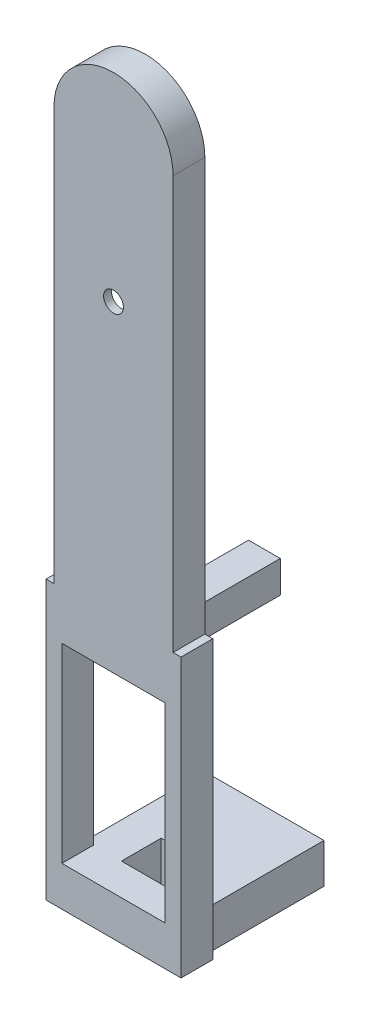
SolidWorks part; units mm, degrees
ref_plane "前基準面" through (0, 0, 0) normal (0, 0, 1) x (1, 0, 0)
ref_plane "上基準面" through (0, 0, 0) normal (0, 1, 0) x (1, 0, 0)
ref_plane "右基準面" through (0, 0, 0) normal (1, 0, 0) x (0, 0, -1)
sketch "草圖1" plane through (0, 0, 0) normal (0, 0, 1) x (1, 0, 0)
  line L0 (0, 0) -> (0, 4.6483) construction
  line L1 (7.5, 0) -> (7.5, 52)
  line L2 (7.5, 0) -> (-7.5, 0)
  line L3 (-7.5, 0) -> (-7.5, 52)
  arc A0 (7.5, 52) -> (-7.5, 52) centre (0, 52) ccw
  dimension "D1" = 7.5
  dimension "D2" = 52
extrude "填料-伸長1" add sketch "草圖1" along normal blind 4
sketch "草圖3" plane through (0, 0, 0) normal (0, 0, 1) x (1, 0, 0)
  line L0 (0, 0) -> (0, 14.8578) construction
  line L1 (7.5, 52) -> (-7.5, 52) construction
  line L2 (7.5, 15) -> (-7.5, 15) construction
  line L3 (7.5, 0) -> (7.5, 52) construction
  line L4 (-7.5, 52) -> (-7.5, 0) construction
  line L6 (7.5, 34.5) -> (5, 34.5) construction
  line L7 (5, 34.5) -> (2.1147, 16.658)
  line L8 (5, 34.5) -> (2.1328, 52)
  line L9 (-2.1328, 52) -> (-5, 34.5)
  line L10 (-5, 34.5) -> (-2.1422, 17)
  line L11 (0, 54.1328) -> (0, 59.5) construction
  line L12 (-5, 34.5) -> (-7.5, 34.5) construction
  arc A0 (7.5, 52) -> (-7.5, 52) centre (0, 52) ccw construction
  arc A1 (-4.7386, 36.0956) -> (-4.7403, 32.9094) centre (0, 34.5) ccw
  arc A2 (-2.1422, 17) -> (2.1147, 16.658) centre (0, 17) ccw
  arc A3 (-2.1328, 52) -> (2.1328, 52) centre (0, 52) cw
  arc A4 (4.7452, 32.9241) -> (4.7386, 36.0956) centre (0, 34.5) ccw
  dimension "D4" = 10
  dimension "D1" = 35
extrude "除料-伸長1" cut sketch "草圖3" along normal blind 3 contours A3 L9 L10 A2 L7 L8
sketch "草圖5" plane through (0, 0, 0) normal (0, 0, 1) x (1, 0, 0)
  line L0 (5, 34.5) -> (-5, 34.5) construction
  circle A0 centre (0, 34.5) radius 1.25
  dimension "D1" = 2.5
extrude "除料-伸長2" cut sketch "草圖5" along normal blind 12.4
sketch "草圖6" plane through (0, 0, 0) normal (0, 0, 1) x (1, 0, 0)
  line L0 (0, 62.3953) -> (0, -4.428) construction
  line L1 (0, -2.2) -> (0, 2.2) construction
  line L3 (8.5, 0) -> (-8.5, 0)
  line L4 (8.5, 0) -> (8.5, -35)
  line L5 (8.5, -35) -> (-8.5, -35)
  line L6 (-8.5, 0) -> (-8.5, -35)
  dimension "D1" = 17
  dimension "D2" = 8.5
  dimension "D3" = 35
extrude "填料-伸長2" add sketch "草圖6" along normal blind 4
sketch "草圖7" plane through (0, 0, 0) normal (0, 0, 1) x (1, 0, 0)
  line L0 (0, 64.1958) -> (0, -38.5274) construction
  line L1 (0, -2.2) -> (0, 2.2) construction
  line L3 (-6.5, -6) -> (6.5, -6)
  line L4 (-6.5, -6) -> (-6.5, -30)
  line L5 (-6.5, -30) -> (6.5, -30)
  line L6 (6.5, -6) -> (6.5, -30)
  line L7 (-8.5, -35) -> (8.5, -35) construction
  dimension "D1" = 6.5
  dimension "D2" = 13
  dimension "D3" = 24
  dimension "D4" = 5
extrude "除料-伸長3" cut sketch "草圖7" along normal blind 12.1
sketch "草圖8" plane through (0, 0, 0) normal (0, 0, 1) x (1, 0, 0)
  line L0 (0, 64.1958) -> (0, -34.8274) construction
  line L1 (0, -2.2) -> (0, 2.2) construction
  line L2 (0, 64.1958) -> (0, -39.0142) construction
  line L3 (6.5, -18) -> (-6.5, -18) construction
  line L4 (6.5, -30) -> (6.5, -6) construction
  line L5 (-6.5, -6) -> (-6.5, -30) construction
  line L6 (6.5, -6) -> (-6.5, -6) construction
  line L7 (2, -2) -> (-2, -2)
  line L8 (2, -2) -> (2, -6)
  line L9 (2, -6) -> (-2, -6)
  line L10 (-2, -2) -> (-2, -6)
  circle A0 centre (0, -4) radius 1.25
  dimension "D5" = 2.5
  dimension "D1" = 4
  dimension "D2" = 4
  dimension "D3" = 2
  dimension "D4" = 2
extrude "填料-伸長3" add sketch "草圖8" against normal blind 15
ref_plane "平面1" through (0, -35, 0) normal (0, 1, 0) x (1, 0, 0)
sketch "草圖9" plane through (0, -35, 0) normal (0, 1, 0) x (1, 0, 0)
  line L0 (0, 15.9246) -> (0, -4.8463) construction
  line L1 (0, -10.45) -> (0, 10.45) construction
  line L2 (-3, 0) -> (-3, 5)
  line L3 (7.5, 0) -> (-7.5, 0) construction
  line L4 (-3, 5) -> (3, 5)
  line L5 (-3, 0) -> (3, 0)
  line L6 (3, 0) -> (3, 5)
  line L7 (7.5, 0) -> (-7.5, 0)
  line L8 (-7.5, 0) -> (7.5, 0) construction
  line L9 (-7.5, 0) -> (-7.5, 15)
  line L14 (-7.5, 15) -> (7.5, 15)
  line L15 (7.5, 0) -> (7.5, 15)
  point P12 (0, 0)
  point P13 (0, 5)
  point P20 (0, 0)
  point P21 (0, 15)
  dimension "D1" = 5
  dimension "D2" = 3
  dimension "D3" = 3
  dimension "D4" = 15
  dimension "D5" = 7.5
extrude "填料-伸長4" add sketch "草圖9" along normal blind 5 contours L0 L14 L9 L7 L2 L4 | L14 L0 L4 L6 L7 L15
sketch "草圖10" plane through (0, 0, 0) normal (0, 0, 1) x (1, 0, 0)
  line L0 (0, 64.1958) -> (0, -35) construction
  line L1 (-7.5, -35) -> (7.5, -35) construction
  line L2 (7.5, -32.5) -> (-7.5, -32.5) construction
  line L3 (7.5, -30) -> (7.5, -35) construction
  line L4 (-7.5, -30) -> (-7.5, -35) construction
  circle A0 centre (0, -32.5) radius 1.25
  dimension "D1" = 2.5
extrude "除料-伸長4" cut sketch "草圖10" against normal blind 35 contours A0
